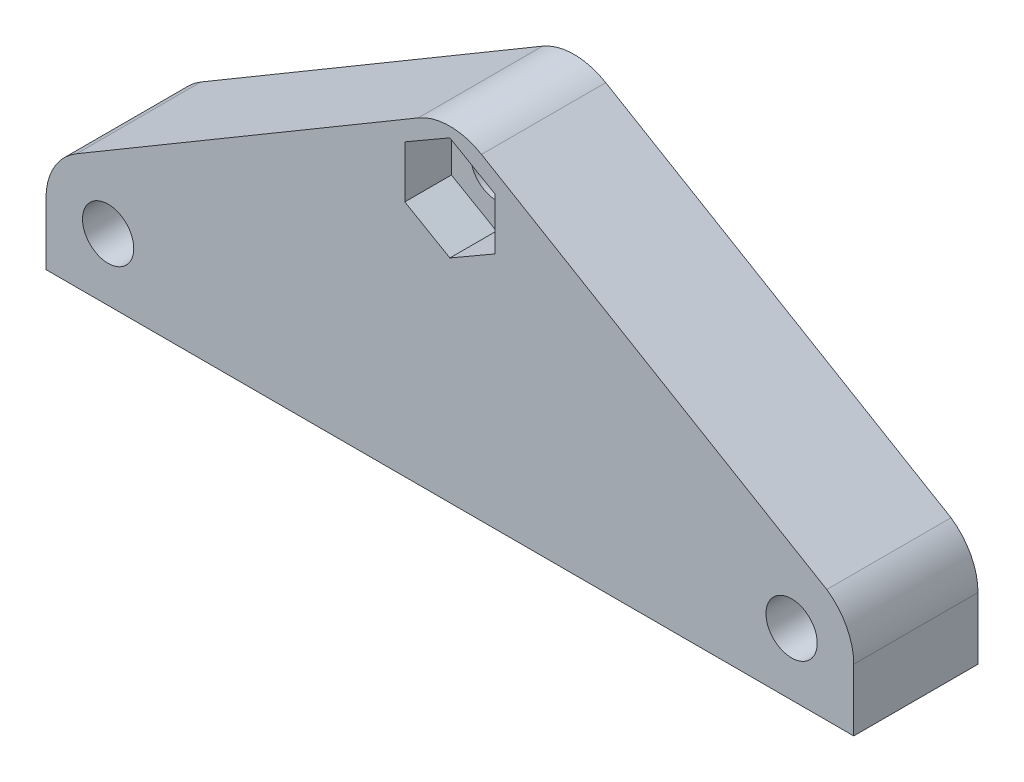
SolidWorks part; units mm, degrees
ref_plane "Front Plane" through (0, 0, 0) normal (0, 0, 1) x (1, 0, 0)
ref_plane "Top Plane" through (0, 0, 0) normal (0, 1, 0) x (1, 0, 0)
ref_plane "Right Plane" through (0, 0, 0) normal (1, 0, 0) x (0, 0, -1)
sketch "Sketch1" plane through (0, 0, 0) normal (0, 0, 1) x (1, 0, 0)
  line L0 (4, 4) -> (48, 4) construction
  line L1 (0, 0) -> (52, 0)
  line L2 (0, 0) -> (0, 4)
  line L3 (23.9651, 20.4437) -> (1.9651, 7.4437)
  line L4 (52, 0) -> (52, 4)
  line L6 (26, 4) -> (26, 17) construction
  line L7 (28.0361, 20.443) -> (50.2616, 7.2993)
  arc A0 (28.0361, 20.443) -> (23.9651, 20.4437) centre (26, 17) ccw
  arc A1 (52, 4) -> (50.2616, 7.2993) centre (48, 4) ccw
  circle A2 centre (26, 17) radius 1.65
  arc A3 (1.9651, 7.4437) -> (0, 4) centre (4, 4) ccw
  circle A4 centre (4, 4) radius 1.65
  circle A5 centre (48, 4) radius 1.65
  dimension "D1" = 44
  dimension "D2" = 4
  dimension "D3" = 3.3
  dimension "D4" = 3.3
  dimension "D8" = 4
  dimension "D5" = 52
  dimension "D6" = 13
  dimension "D7" = 4
extrude "Boss-Extrude1" add sketch "Sketch1" along normal blind 8
sketch "Sketch2" plane through (0, 0, 8) normal (0, 0, 1) x (1, 0, 0)
  line L1 (26, 13.6514) -> (28.9, 15.3257)
  line L2 (28.9, 15.3257) -> (28.9, 18.6743)
  line L3 (28.9, 18.6743) -> (26, 20.3486)
  line L4 (26, 20.3486) -> (23.1, 18.6743)
  line L5 (23.1, 18.6743) -> (23.1, 15.3257)
  line L6 (23.1, 15.3257) -> (26, 13.6514)
  circle A0 centre (26, 17) radius 2.9 construction
  circle A2 centre (26, 17) radius 1.65 construction
  dimension "D1" = 5.8
extrude "Cut-Extrude1" cut sketch "Sketch2" against normal blind 3
